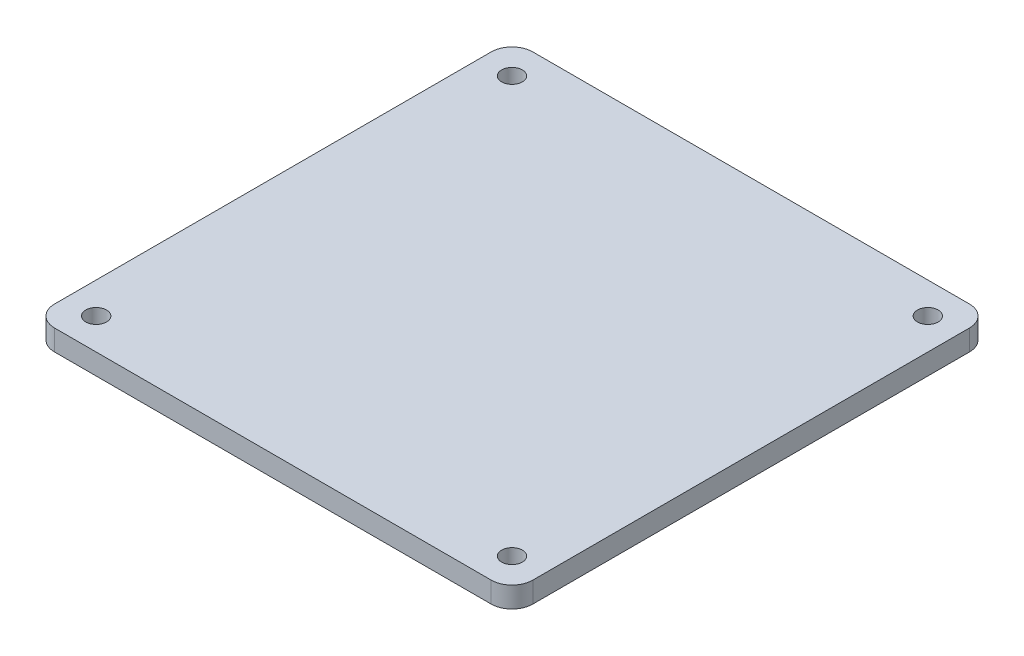
SolidWorks part; units mm, degrees
ref_plane "Front Plane" through (0, 0, 0) normal (0, 0, 1) x (1, 0, 0)
ref_plane "Top Plane" through (0, 0, 0) normal (0, 1, 0) x (1, 0, 0)
ref_plane "Right Plane" through (0, 0, 0) normal (1, 0, 0) x (0, 0, -1)
sketch "Sketch1" plane through (0, 0, 0) normal (0, 1, 0) x (1, 0, 0)
  line L1 (-21, 23) -> (21, 23)
  line L2 (-23, 21) -> (-23, -21)
  line L3 (-21, -23) -> (21, -23)
  line L4 (23, 21) -> (23, -21)
  line L5 (-23, 23) -> (23, -23) construction
  line L6 (-23, -23) -> (23, 23) construction
  arc A0 (23, 21) -> (21, 23) centre (21, 21) ccw
  arc A1 (23, -21) -> (21, -23) centre (21, -21) cw
  arc A2 (-21, -23) -> (-23, -21) centre (-21, -21) cw
  arc A3 (-23, 21) -> (-21, 23) centre (-21, 21) cw
  circle A4 centre (-20, 20) radius 1
  circle A5 centre (20, 20) radius 1
  circle A6 centre (-20, -20) radius 1
  circle A7 centre (20, -20) radius 1
  point P0 (0, 0)
  dimension "D3" = 3
  dimension "D4" = 3
  dimension "D5" = 3
  dimension "D6" = 3
  dimension "D1" = 46
  dimension "D2" = 46
extrude "Boss-Extrude1" add sketch "Sketch1" along normal blind 2
